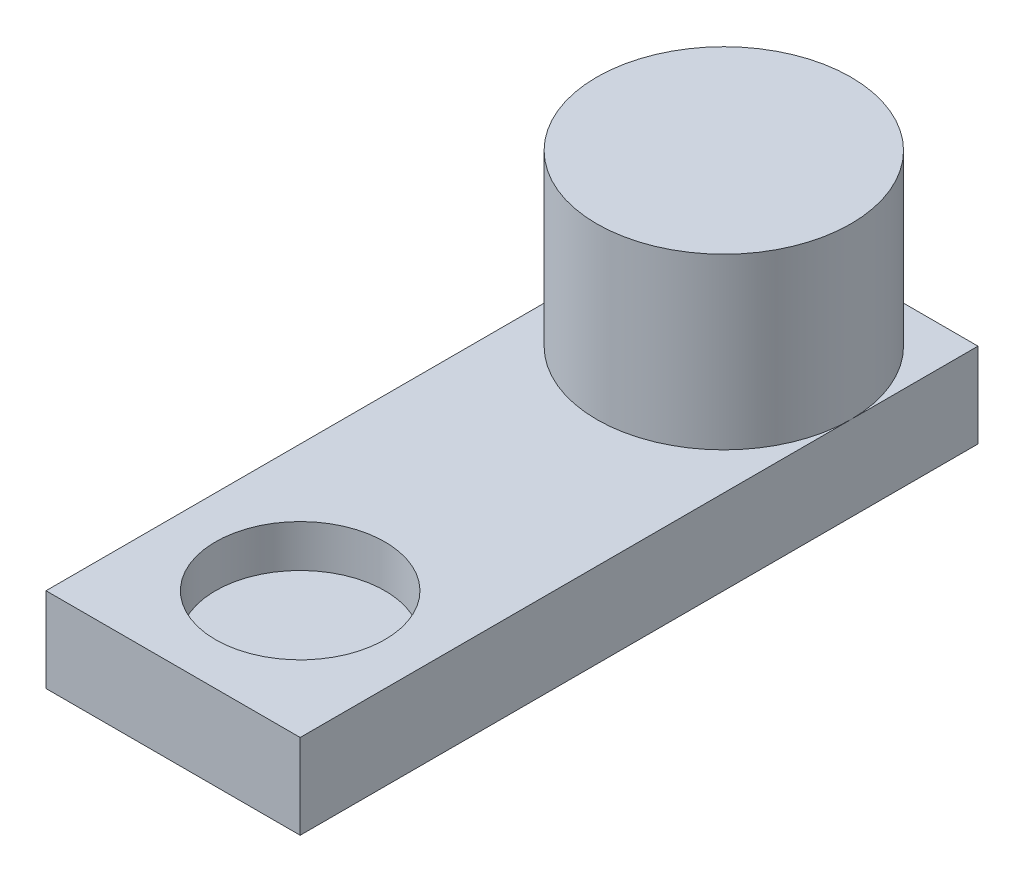
SolidWorks part; units mm, degrees
ref_plane "Front Plane" through (0, 0, 0) normal (0, 0, 1) x (1, 0, 0)
ref_plane "Top Plane" through (0, 0, 0) normal (0, 1, 0) x (1, 0, 0)
ref_plane "Right Plane" through (0, 0, 0) normal (1, 0, 0) x (0, 0, -1)
sketch "Sketch1" plane through (0, 0, 0) normal (0, 1, 0) x (1, 0, 0)
  line L1 (-15, -40) -> (15, -40)
  line L2 (-15, -40) -> (-15, 40)
  line L3 (-15, 40) -> (15, 40)
  line L4 (15, -40) -> (15, 40)
  line L5 (-15, -40) -> (15, 40) construction
  line L6 (-15, 40) -> (15, -40) construction
  point P0 (0, 0)
  dimension "D1" = 80
  dimension "D2" = 30
extrude "Boss-Extrude1" add sketch "Sketch1" along normal blind 10
sketch "Sketch2" plane through (0, 10, 0) normal (0, 1, 0) x (1, 0, 0)
  line L0 (15, 40) -> (-15, 40) construction
  line L1 (-15, 40) -> (-15, -40) construction
  circle A0 centre (0, 25) radius 15
  point P8 (0, -25.853)
  point P9 (3.7533, -25.211)
  dimension "D1" = 30
extrude "Boss-Extrude2" add sketch "Sketch2" along normal blind 20
sketch "Sketch3" plane through (0, 10, 0) normal (0, 1, 0) x (1, 0, 0)
  line L0 (-15, 25) -> (-15, -40) construction
  line L1 (-15, -40) -> (15, -40) construction
  circle A0 centre (0, -25) radius 10
  dimension "D1" = 20
  dimension "D2" = 15
  dimension "D3" = 15
extrude "Cut-Extrude1" cut sketch "Sketch3" against normal blind 5
equation "\"D3@Sketch3\"=\"D2@Sketch3\""
